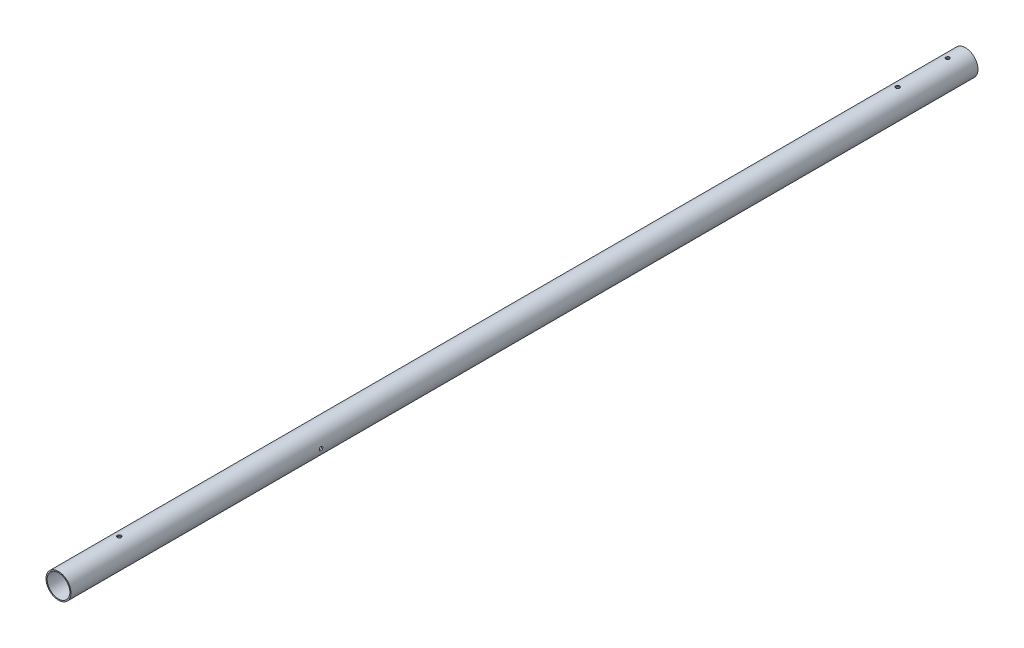
SolidWorks part; units mm, degrees
material "1060 Alloy"
ref_plane "Front Plane" through (0, 0, 0) normal (0, 0, 1) x (1, 0, 0)
ref_plane "Top Plane" through (0, 0, 0) normal (0, 1, 0) x (1, 0, 0)
ref_plane "Right Plane" through (0, 0, 0) normal (1, 0, 0) x (0, 0, -1)
sketch "Sketch2" plane through (0, 0, 0) normal (0, 0, 1) x (1, 0, 0)
  circle A0 centre (0, 0) radius 17.5
  circle A1 centre (0, 0) radius 15.9125
  dimension "D1" = 35
  dimension "D2" = 31.825
extrude "Boss-Extrude1" add sketch "Sketch2" along normal mid plane 1080
sketch "Sketch4" plane through (0, 0, 0) normal (0, 1, 0) x (1, 0, 0)
  line L0 (0, 540) -> (0, 525) construction
  line L1 (17.5, 540) -> (-17.5, 540) construction
  dimension "D1" = 15
hole_wizard "M5 Clearance Hole1" positions "Sketch5" profile "Sketch6" hole size "M5" standard "AS"
sketch "Sketch5" plane through (0, 0, 0) normal (0, 1, 0) x (1, 0, 0)
  line L2 (0, 540) -> (0, 445)
  line L3 (15.9125, 540) -> (-15.9125, 540) construction
  point P0 (0, 445)
  dimension "D1" = 95
sketch "Sketch6" plane through (0, 0, -445) normal (1, 0, 0) x (0, 0, -1)
  line L0 (0, 0) -> (0, 17.5)
  line L1 (0, 17.5) -> (2.75, 17.5)
  line L2 (2.75, 17.5) -> (2.75, 0)
  line L5 (2.75, 0) -> (0, 0)
  line L11 (0, -6.35) -> (0, 107.95) construction
  dimension "Thru Hole Dia." = 5.5
  dimension "Thru Hole Depth" = 17.5
mirror "Mirror1" about plane through (0, 0, 0) normal (0, 1, 0) of "M5 Clearance Hole1"
sketch "Sketch7" plane through (0, 0, 540) normal (0, 0, 1) x (1, 0, 0)
  circle A0 centre (0, 0) radius 17.5
  circle A1 centre (0, 0) radius 15.9125
  circle A2 centre (0, 0) radius 17.5 construction
  circle A3 centre (0, 0) radius 15.9125 construction
extrude "Boss-Extrude2" add sketch "Sketch7" along normal blind 130
sketch "Sketch9" plane through (0, 0, 670) normal (0, 0, 1) x (1, 0, 0)
  circle A0 centre (0, 0) radius 17.5
  circle A1 centre (0, 0) radius 17.5 construction
sketch "Sketch13" plane through (0, 0, 670) normal (0, 0, 1) x (1, 0, 0)
  circle A0 centre (0, 0) radius 17.5
  circle A1 centre (0, 0) radius 15.9125
  circle A2 centre (0, 0) radius 17.5 construction
  circle A3 centre (0, 0) radius 15.9125 construction
extrude "Boss-Extrude4" add sketch "Sketch13" along normal up to surface (59.5 mm away)
sketch "Sketch12" plane through (0, 0, 0) normal (0, 1, 0) x (1, 0, 0)
  line L2 (-17.5, 540) -> (-17.5, -729.5) construction
  line L3 (-15.9125, -729.5) -> (15.9125, -729.5) construction
  circle A0 centre (0, -644.5) radius 2.75
  circle A1 centre (0, -644.5) radius 2.75 construction
  dimension "D2" = 17.5
  dimension "D1" = 85
extrude "Cut-Extrude4" cut sketch "Sketch12" against normal through all both and the other way through all
sketch "Sketch14" plane through (0, 0, 0) normal (0, 1, 0) x (1, 0, 0)
  line L0 (0, 540) -> (0, 515) construction
  line L1 (15.9125, 540) -> (-15.9125, 540) construction
  circle A0 centre (0, 515) radius 2.5
  dimension "D1" = 5
  dimension "D2" = 25
extrude "Cut-Extrude5" cut sketch "Sketch14" against normal through all both and the other way through all
sketch "Sketch15" plane through (0, 0, 0) normal (1, 0, 0) x (0, 0, -1)
  line L1 (-629.5, -19.0875) -> (-629.5, 19.0875) construction
  circle A0 centre (-379.5, 0) radius 2.5
  dimension "D1" = 5
  dimension "D2" = 250
extrude "Cut-Extrude6" cut sketch "Sketch15" against normal through all both and the other way through all
equation "\"frontTubeLength\"= 1200mm"
equation "\"outDiameter\"= 35mm"
equation "\"keelOutDiameter\"= 1in"
equation "\"bottomTubeLength\"= \"frontTubeLength\"*0.9"
equation "\"D1@Sketch2\"=\"outDiameter\""
equation "\"D2@Sketch2\"=\"outDiameter\"-0.125in"
equation "\"D1@Boss-Extrude1\"=\"bottomTubeLength\""
equation "\"D2@Sketch12\"=\"outDiameter\"/2"
equation "\"boltDiameter\"= 5mm"
equation "\"D1@Sketch15\"=\"boltDiameter\""
